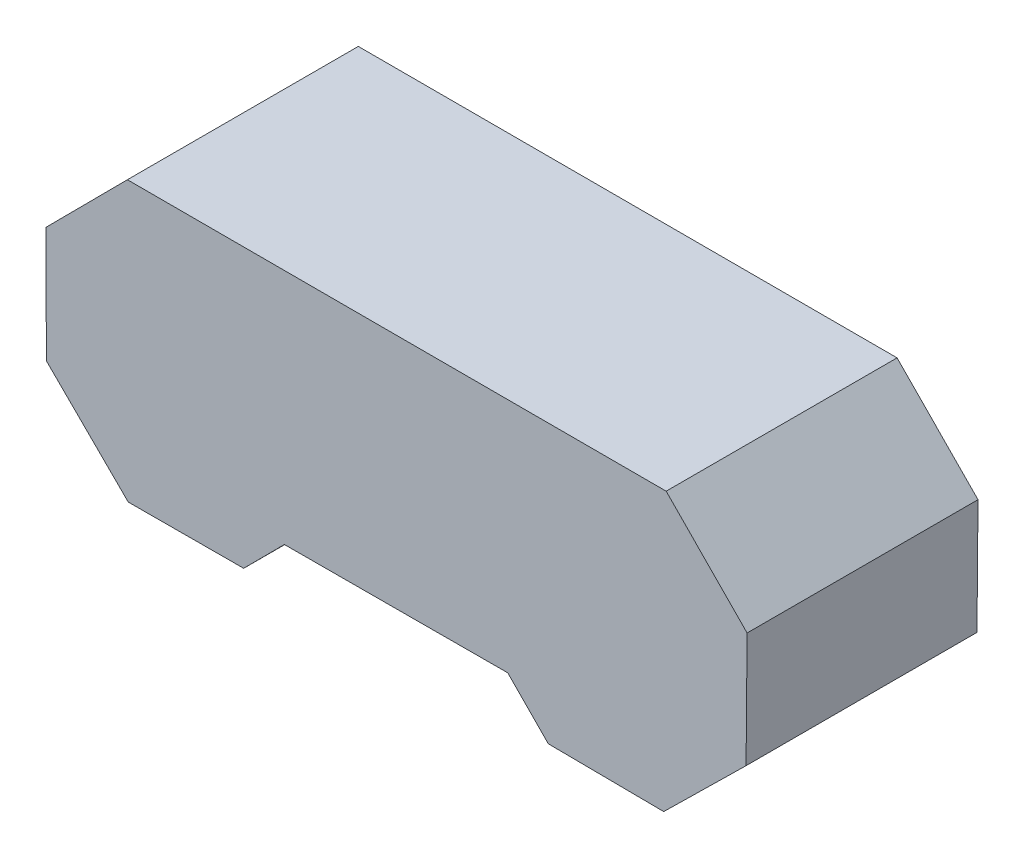
SolidWorks part; units mm, degrees
ref_plane "Front Plane" through (0, 0, 0) normal (0, 0, 1) x (1, 0, 0)
ref_plane "Top Plane" through (0, 0, 0) normal (0, 1, 0) x (1, 0, 0)
ref_plane "Right Plane" through (0, 0, 0) normal (1, 0, 0) x (0, 0, -1)
sketch "Sketch1" plane through (0, 0, 0) normal (0, 0, 1) x (1, 0, 0)
  line L0 (60.1346, -64.4421) -> (-87.3197, -64.8179)
  line L1 (-190.9434, 91.8953) -> (164.6566, 91.6733)
  line L2 (-244.4288, -38.3556) -> (-190.3805, -92.0741)
  line L3 (-190.3805, -92.0741) -> (-114.1779, -91.8409)
  line L4 (-114.1779, -91.8409) -> (-87.3197, -64.8179)
  line L8 (-190.9434, 91.8953) -> (-244.6619, 37.847)
  line L9 (-244.6619, 37.847) -> (-244.4288, -38.3556)
  line L10 (163.0372, -92.2898) -> (217.393, -38.8826)
  line L11 (217.393, -38.8826) -> (218.0638, 37.3174)
  line L12 (218.0638, 37.3174) -> (164.6566, 91.6733)
  line L16 (60.1346, -64.4421) -> (86.8372, -91.619)
  line L17 (86.8372, -91.619) -> (163.0372, -92.2898)
  line L18 (34.014, 29.0834) -> (33.3657, -44.5609) [skipped]
  line L19 (81.4278, 85.438) -> (28.895, 33.822) [skipped]
  line L20 (-60.6926, 38.4099) -> (-112.9281, 90.3267) [skipped]
  line L21 (-60.4594, -37.7927) -> (-60.6848, 35.8541) [skipped]
  line L22 (-114.7408, 92.1284) -> (-188.3876, 91.9031) [skipped]
  line L23 (154.8031, 91.76) -> (81.1588, 92.4083) [skipped]
  circle A0 centre (-152.5607, 0.0272) radius 91.9851 construction
  circle A1 centre (125.7469, 0.0272) radius 91.9851 construction
  dimension "D1" = 355.6
  dimension "D2" = 76.2
  dimension "D3" = 38.1
  dimension "D4" = 134.531
  dimension "D5" = 147.4543
extrude "Boss-Extrude1" add sketch "Sketch1" along normal blind 152.4
